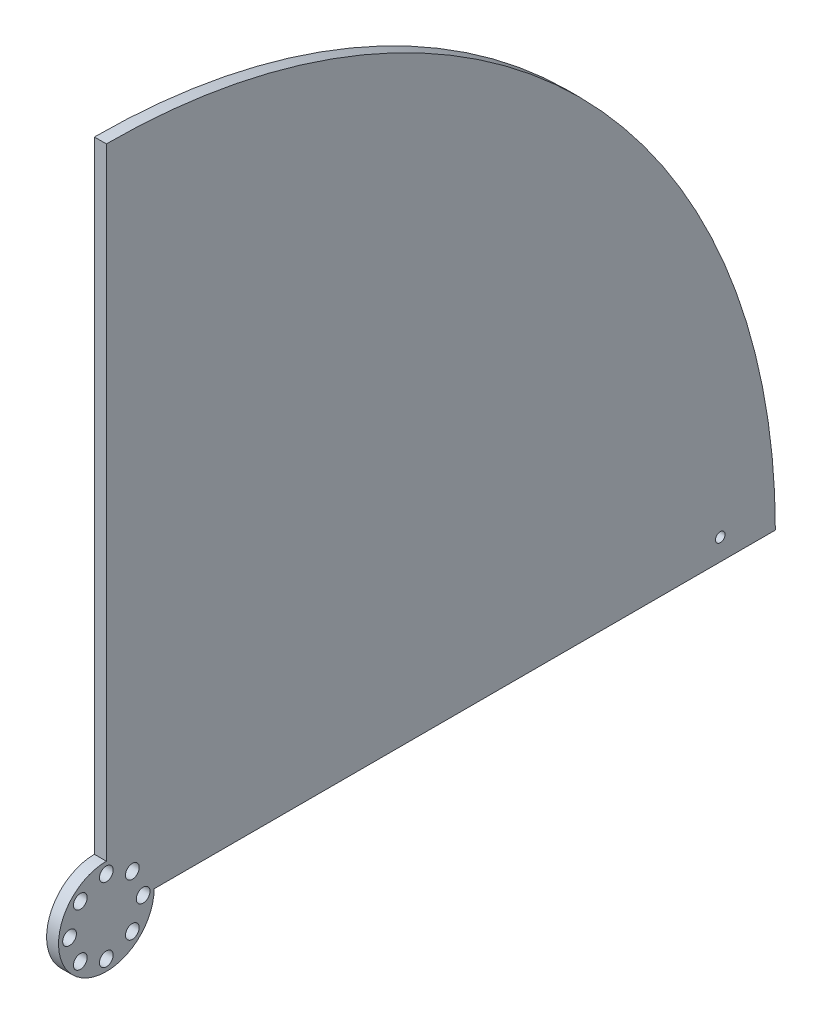
SolidWorks part; units mm, degrees
ref_plane "Front" through (0, 0, 0) normal (0, 0, 1) x (1, 0, 0)
ref_plane "Top" through (0, 0, 0) normal (0, 1, 0) x (1, 0, 0)
ref_plane "Right" through (0, 0, 0) normal (1, 0, 0) x (0, 0, -1)
sketch "Sketch1" plane through (0, 0, 0) normal (1, 0, 0) x (0, 0, -1)
  line L0 (0, 177.8) -> (0, 0)
  line L1 (0, 0) -> (177.8, 0)
  arc A0 (177.8, 0) -> (0, 177.8) centre (0, 0) ccw
  dimension "D1" = 355.6
extrude "Boss-Extrude1" add sketch "Sketch1" along normal blind 3.175
sketch "Sketch2" plane through (3.175, 0, 0) normal (1, 0, 0) x (0, 0, -1)
  line L0 (0, 0) -> (0, 12.7)
  line L1 (0, 0) -> (12.7, 0)
  arc A0 (0, 12.7) -> (12.7, 0) centre (0, 0) ccw
  dimension "D1" = 25.4
extrude "Boss-Extrude2" add sketch "Sketch2" against normal blind 3.175
sketch "Sketch3" plane through (3.175, 0, 0) normal (1, 0, 0) x (0, 0, -1)
  line L0 (0, 0) -> (0, 9.779) construction
  circle A0 centre (0, 9.779) radius 1.8288
  circle A1 centre (6.9148, 6.9148) radius 1.8288
  circle A2 centre (9.779, 0) radius 1.8288
  circle A3 centre (6.9148, -6.9148) radius 1.8288
  circle A4 centre (0, -9.779) radius 1.8288
  circle A5 centre (-6.9148, -6.9148) radius 1.8288
  circle A6 centre (-9.779, 0) radius 1.8288
  circle A7 centre (-6.9148, 6.9148) radius 1.8288
  point P20 (0, 0)
  dimension "D2" = 3.6576
  dimension "D1" = 9.779
  dimension "D3" = 8
extrude "Cut-Extrude1" cut sketch "Sketch3" against normal through all
sketch "Sketch5" plane through (3.175, 0, 0) normal (1, 0, 0) x (0, 0, -1)
  line L0 (0, 0) -> (163.159, 5.6976) construction
  line L1 (12.7, 0) -> (177.8, 0) construction
  circle A0 centre (163.159, 5.6976) radius 1.27
  dimension "D3" = 2.54
  dimension "D1" = 163.2585
  dimension "D2" = 2
extrude "Cut-Extrude2" cut sketch "Sketch5" against normal through all
